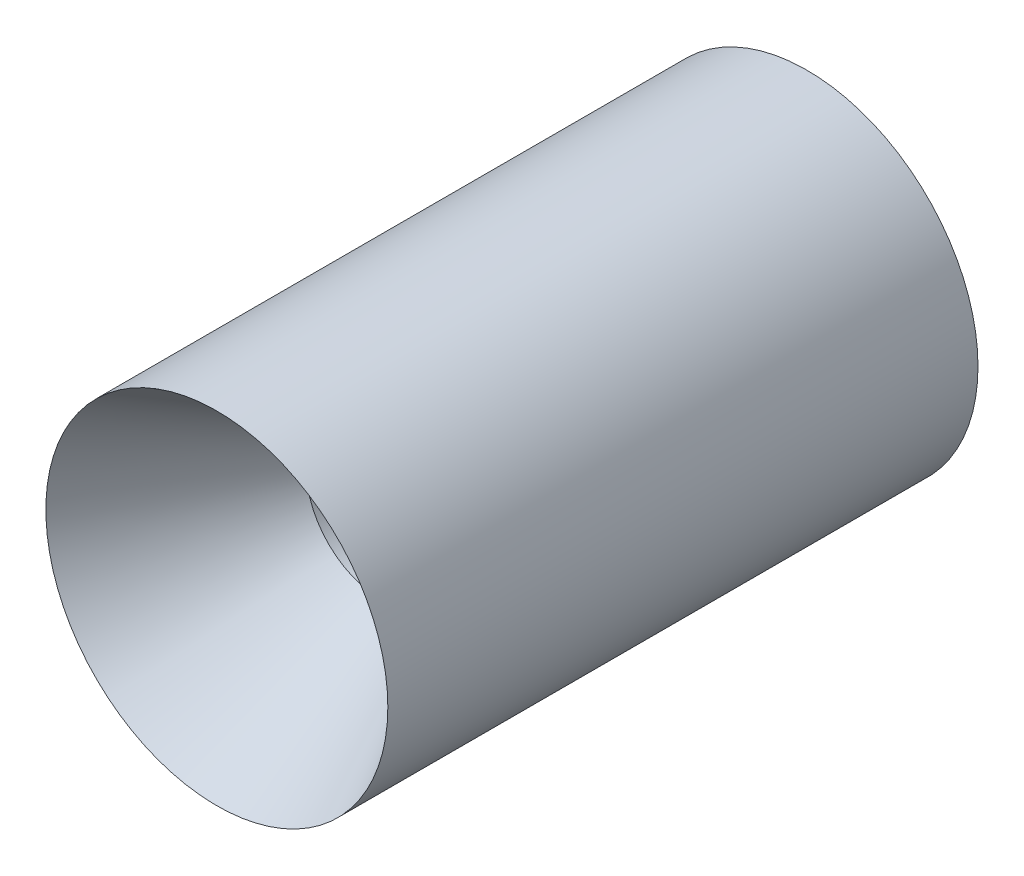
SolidWorks part; units mm, degrees
material "C (Graphite)"
ref_plane "Front Plane" through (0, 0, 0) normal (0, 0, 1) x (1, 0, 0)
ref_plane "Top Plane" through (0, 0, 0) normal (0, 1, 0) x (1, 0, 0)
ref_plane "Right Plane" through (0, 0, 0) normal (1, 0, 0) x (0, 0, -1)
sketch "Sketch3" plane through (0, 0, 0) normal (1, 0, 0) x (0, 0, -1)
  line L0 (0, 0) -> (77.1711, 0) construction
  line L5 (49.53, 12.7208) -> (49.53, 14.351)
  line L6 (49.53, 14.351) -> (0, 14.351)
  line L9 (19.5576, 6.35) -> (13.8581, 6.35)
  line L11 (0, 14.351) -> (13.8581, 6.35)
  line L12 (19.5576, 6.35) -> (49.53, 12.7208)
  dimension "D1" = 12.7208
  dimension "D2" = 30
  dimension "D3" = 12
  dimension "D4" = 49.53
  dimension "D5" = 6.35
  dimension "D7" = 14.351
revolve "Revolve1" add sketch "Sketch3" angle 360 about L0
